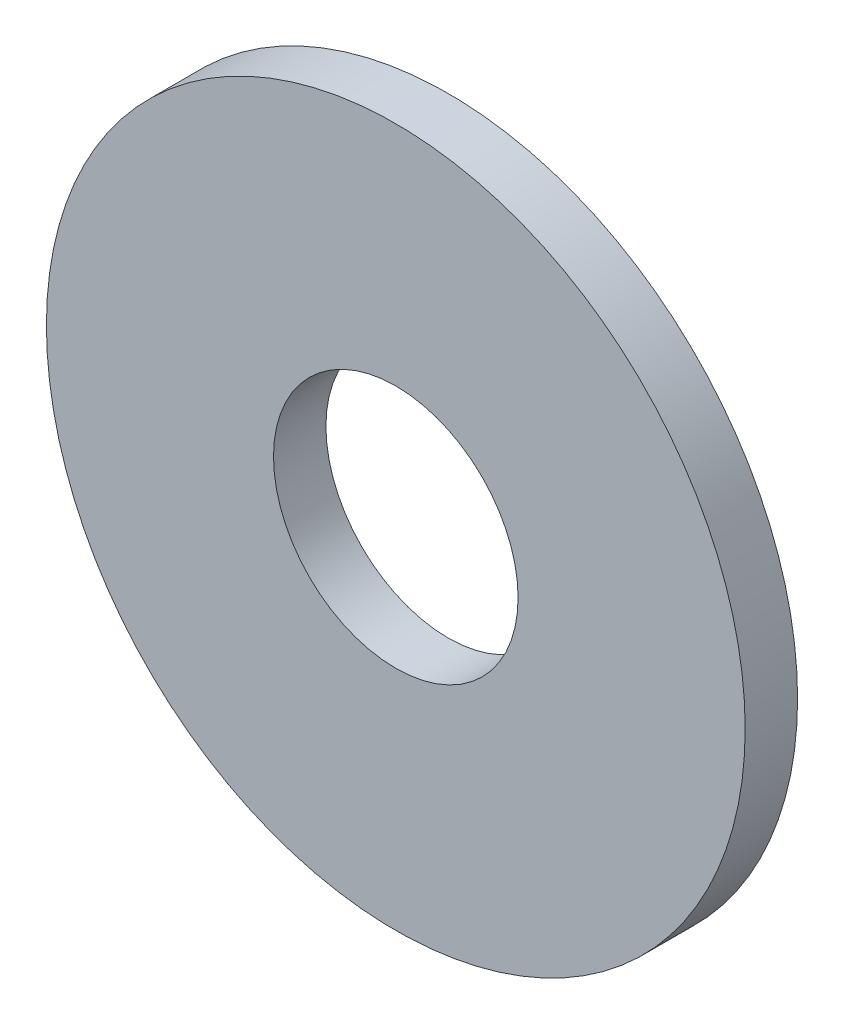
SolidWorks part; units mm, degrees
material "AISI 304"
ref_plane "Front Plane" through (0, 0, 0) normal (0, 0, 1) x (1, 0, 0)
ref_plane "Top Plane" through (0, 0, 0) normal (0, 1, 0) x (1, 0, 0)
ref_plane "Right Plane" through (0, 0, 0) normal (1, 0, 0) x (0, 0, -1)
sketch "Sketch1" plane through (0, 0, 0) normal (0, 0, 1) x (1, 0, 0)
  circle A0 centre (0, 0) radius 4.2
  circle A1 centre (0, 0) radius 12
  dimension "ID" = 8.4
  dimension "OD" = 24
extrude "Extrude1" add sketch "Sketch1" against normal blind 1.8
